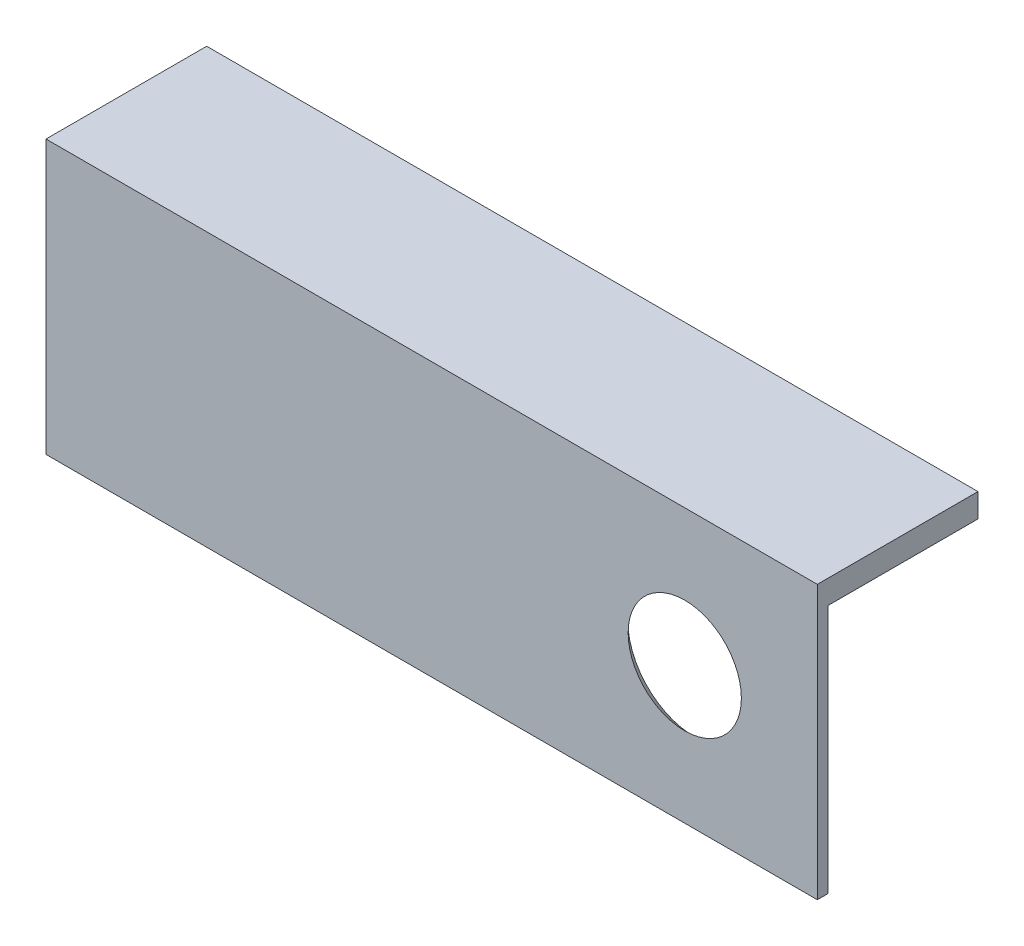
SolidWorks part; units mm, degrees
ref_plane "Alzado" through (0, 0, 0) normal (0, 0, 1) x (1, 0, 0)
ref_plane "Planta" through (0, 0, 0) normal (0, 1, 0) x (1, 0, 0)
ref_plane "Vista lateral" through (0, 0, 0) normal (1, 0, 0) x (0, 0, -1)
sketch "Croquis1" plane through (0, 0, 0) normal (0, 0, 1) x (1, 0, 0)
  line L1 (-24, 8.5) -> (24, 8.5)
  line L2 (-24, 8.5) -> (-24, -8.5)
  line L3 (-24, -8.5) -> (24, -8.5)
  line L4 (24, 8.5) -> (24, -8.5)
  line L5 (-24, 8.5) -> (24, -8.5) construction
  line L6 (-24, -8.5) -> (24, 8.5) construction
  point P0 (0, 0)
  dimension "D1" = 48
  dimension "D2" = 17
extrude "Saliente-Extruir1" add sketch "Croquis1" along normal blind 10
sketch "Croquis2" plane through (0, 0, 10) normal (0, 0, 1) x (1, 0, 0)
  line L0 (0, 16.0015) -> (0, -18.026) construction
  line L1 (-29.4334, 0) -> (28.8105, 0) construction
sketch "Croquis7" plane through (-24, 0, 0) normal (-1, 0, 0) x (0, 0, 1)
  line L0 (0, 7.0242) -> (9.3461, 7.0242)
  line L1 (0, 8.5) -> (0, -8.5) construction
  line L2 (9.3461, 7.0242) -> (9.3461, -8.5)
  line L3 (10, -8.5) -> (0, -8.5) construction
  line L4 (9.3461, -8.5) -> (0, -8.5)
  line L5 (0, -8.5) -> (0, 7.0242)
extrude "Cortar-Extruir1" cut sketch "Croquis7" against normal through all
sketch "Croquis8" plane through (0, 0, 9.3461) normal (0, 0, -1) x (-1, 0, 0)
  line L0 (29.4334, 0) -> (-28.8105, 0) construction
  line L1 (-24, -8.5) -> (-24, 7.0242) construction
  circle A0 centre (18.0985, 0) radius 3
  circle A1 centre (9.0985, 0) radius 3
  circle A2 centre (-16, 0) radius 4 construction
  dimension "D1" = 9
  dimension "D2" = 8
hole_wizard "Taladro de margen para M3.53" positions "Croquis11" profile "Croquis12" hole size "M3.5" standard "KS" end condition through all
sketch "Croquis11" plane through (0, 0, 9.3461) normal (0, 0, -1) x (-1, 0, 0)
  line L0 (29.4334, 0) -> (-28.8105, 0) construction
  point P0 (-15.7508, 0)
sketch "Croquis12" plane through (15.7508, 0, 9.3461) normal (1, 0, 0) x (0, 1, 0)
  line L0 (0, 0) -> (0, 0.6539)
  line L1 (0, 0.6539) -> (1.95, 0.6539)
  line L2 (1.95, 0.6539) -> (1.95, 2.1728)
  line L3 (1.95, 2.1728) -> (4.2, 0)
  line L5 (4.2, 0) -> (0, 0)
  line L6 (-1.95, 2.1728) -> (-4.2, 0) construction
  line L11 (0, -6.35) -> (0, 107.95) construction
  dimension "Diámetro de taladro hasta el siguiente" = 3.9
  dimension "Profundidad de taladro hasta el siguiente" = 0.6539
  dimension "Diámetro de avellanado cercano" = 8.4
  dimension "Ángulo de avellanado cercano" = 92
